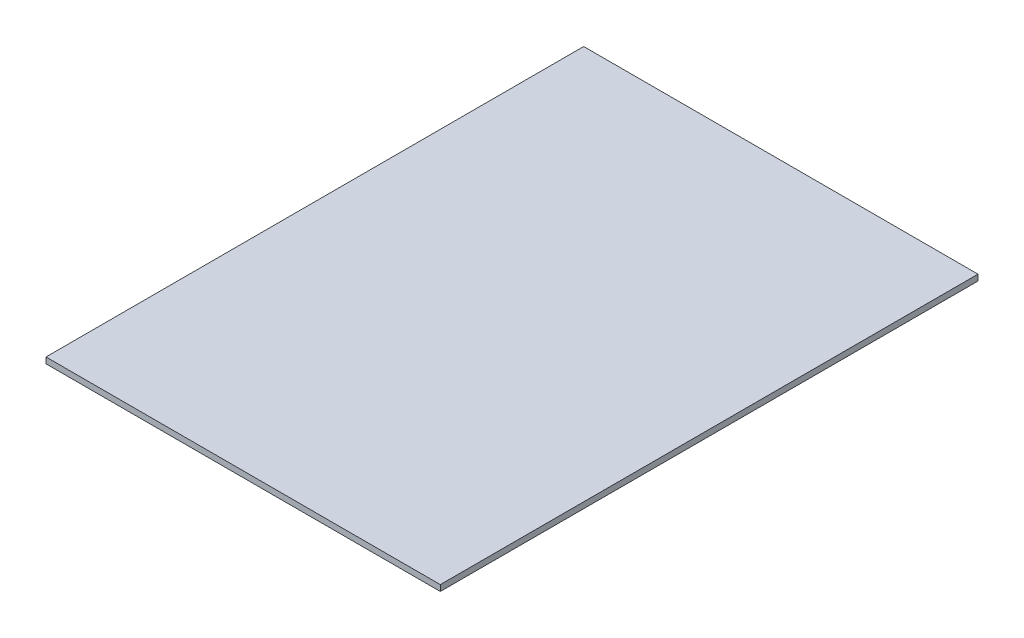
SolidWorks part; units mm, degrees
ref_plane "Front Plane" through (0, 0, 0) normal (0, 0, 1) x (1, 0, 0)
ref_plane "Top Plane" through (0, 0, 0) normal (0, 1, 0) x (1, 0, 0)
ref_plane "Right Plane" through (0, 0, 0) normal (1, 0, 0) x (0, 0, -1)
sketch "Sketch1" plane through (0, 0, 0) normal (0, 1, 0) x (1, 0, 0)
  line L1 (0, 0) -> (1676.4, 0)
  line L2 (0, 0) -> (0, -2286)
  line L3 (0, -2286) -> (1676.4, -2286)
  line L4 (1676.4, 0) -> (1676.4, -2286)
extrude "Boss-Extrude1" add sketch "Sketch1" along normal blind 25.4
